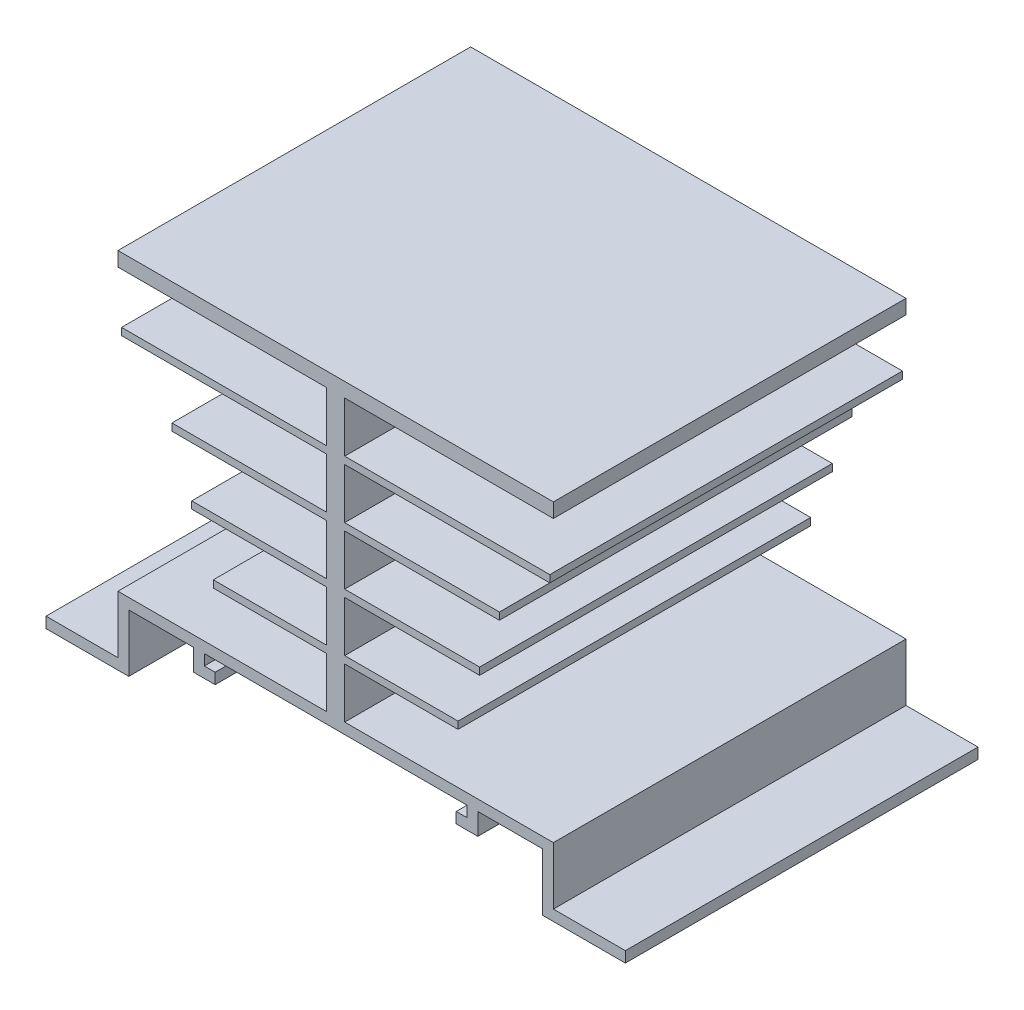
SolidWorks part; units mm, degrees
ref_plane "Front Plane" through (0, 0, 0) normal (0, 0, 1) x (1, 0, 0)
ref_plane "Top Plane" through (0, 0, 0) normal (0, 1, 0) x (1, 0, 0)
ref_plane "Right Plane" through (0, 0, 0) normal (1, 0, 0) x (0, 0, -1)
sketch "Sketch1" plane through (0, 0, 0) normal (0, 0, 1) x (1, 0, 0)
  line L1 (-30.25, -21.25) -> (30.25, -21.25)
  line L2 (-30.25, -21.25) -> (-30.25, 21.25)
  line L3 (-30.25, 21.25) -> (30.25, 21.25)
  line L4 (30.25, -21.25) -> (30.25, 21.25)
  line L5 (-30.25, -21.25) -> (30.25, 21.25) construction
  line L6 (-30.25, 21.25) -> (30.25, -21.25) construction
  point P0 (0, 0)
  dimension "D1" = 60.5
  dimension "D2" = 42.5
extrude "Boss-Extrude1" add sketch "Sketch1" along normal mid plane 49
sketch "Sketch2" plane through (0, 0, 24.5) normal (0, 0, 1) x (1, 0, 0)
  line L0 (-30.25, -21.25) -> (-30.25, -27.75)
  line L1 (-30.25, -27.75) -> (-40.25, -27.75)
  line L2 (-40.25, -27.75) -> (-40.25, -29.25)
  line L3 (-40.25, -29.25) -> (-28.75, -29.25)
  line L4 (-28.75, -29.25) -> (-28.75, -21.25)
  line L5 (-30.25, -21.25) -> (30.25, -21.25) construction
  line L6 (-28.75, -21.25) -> (-30.25, -21.25)
  line L7 (-19.75, -21.25) -> (-19.75, -24.25)
  line L8 (-19.75, -24.25) -> (-16.75, -24.25)
  line L9 (-16.75, -24.25) -> (-16.75, -22.75)
  line L10 (-16.75, -22.75) -> (-18.25, -22.75)
  line L11 (-18.25, -22.75) -> (-18.25, -21.25)
  line L12 (-18.25, -21.25) -> (-19.75, -21.25)
  dimension "D1" = 1.5
  dimension "D2" = 1.5
  dimension "D3" = 8
  dimension "D4" = 11.5
  dimension "D5" = 9
  dimension "D6" = 1.5
  dimension "D7" = 3
  dimension "D8" = 3
  dimension "D9" = 1.5
extrude "Boss-Extrude2" add sketch "Sketch2" against normal up to surface (49 mm away) up to face at (0, 0, -24.5)
sketch "Sketch3" plane through (0, 0, 24.5) normal (0, 0, 1) x (1, 0, 0)
  line L1 (30.25, 21.25) -> (-30.25, 21.25) construction
  line L2 (-30.25, 19.25) -> (-30.25, -19.75)
  line L3 (-30.25, 21.25) -> (-30.25, -27.75) construction
  line L4 (-30.25, -19.75) -> (-1.25, -19.75)
  line L5 (-1.25, -19.75) -> (-1.25, -12.75)
  line L6 (-1.25, -12.75) -> (-17, -12.75)
  line L7 (-17, -12.75) -> (-17, -11.75)
  line L8 (-17, -11.75) -> (-1.25, -11.75)
  line L9 (-1.25, -11.75) -> (-1.25, -4.75)
  line L10 (-1.25, -4.75) -> (-20, -4.75)
  line L11 (-20, -4.75) -> (-20, -3.75)
  line L12 (-20, -3.75) -> (-1.25, -3.75)
  line L13 (-1.25, -3.75) -> (-1.25, 3.25)
  line L14 (-1.25, 3.25) -> (-22.75, 3.25)
  line L15 (-22.75, 3.25) -> (-22.75, 4.25)
  line L16 (-22.75, 4.25) -> (-1.25, 4.25)
  line L17 (-1.25, 4.25) -> (-1.25, 11.25)
  line L18 (-1.25, 11.25) -> (-29.75, 11.25)
  line L19 (-29.75, 11.25) -> (-29.75, 12.25)
  line L20 (-29.75, 12.25) -> (-1.25, 12.25)
  line L21 (-1.25, 12.25) -> (-1.25, 19.25)
  line L22 (-1.25, 19.25) -> (-30.25, 19.25)
  line L24 (-28.75, -21.25) -> (-19.75, -21.25) construction
  line L25 (0, 0) -> (0, 14.2256) construction
  point P31 (0, 0)
  dimension "D1" = 1.5
  dimension "D2" = 1
  dimension "D3" = 2
  dimension "D4" = 1.25
  dimension "D5" = 34
  dimension "D6" = 40
  dimension "D7" = 45.5
  dimension "D8" = 59.5
extrude "Cut-Extrude1" cut sketch "Sketch3" against normal through all
mirror "Mirror1" about plane through (0, 0, 0) normal (1, 0, 0) of "Cut-Extrude1", "Boss-Extrude2"
